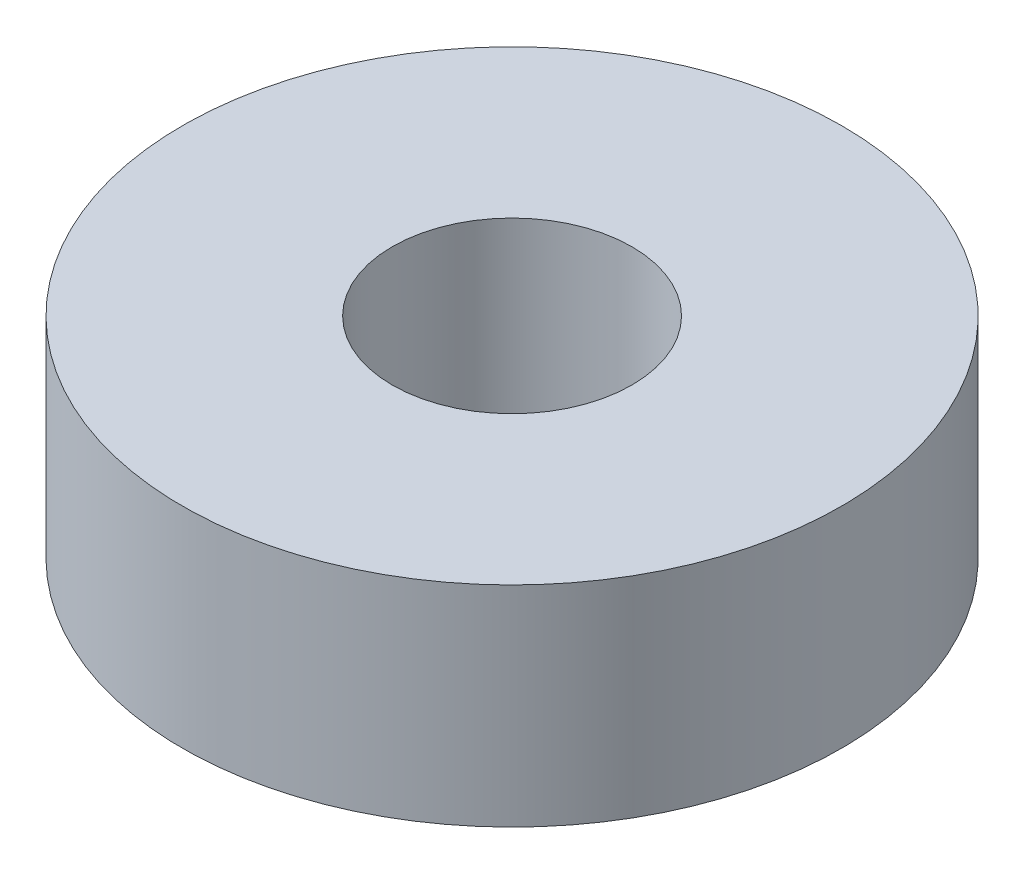
SolidWorks part; units mm, degrees
material "Plain Carbon Steel"
ref_plane "Front Plane" through (0, 0, 0) normal (0, 0, 1) x (1, 0, 0)
ref_plane "Top Plane" through (0, 0, 0) normal (0, 1, 0) x (1, 0, 0)
ref_plane "Right Plane" through (0, 0, 0) normal (1, 0, 0) x (0, 0, -1)
sketch "Sketch1" plane through (0, 0, 0) normal (0, 0, 1) x (1, 0, 0)
  line L0 (0, 0) -> (0, 3.371) construction
  line L1 (4, 0) -> (11, 0)
  line L2 (4, 0) -> (4, 7)
  line L3 (4, 7) -> (11, 7)
  line L4 (11, 0) -> (11, 7)
  dimension "D1" = 8
  dimension "D2" = 22
  dimension "D3" = 7
revolve "Revolve1" add sketch "Sketch1" angle 360 about L0
